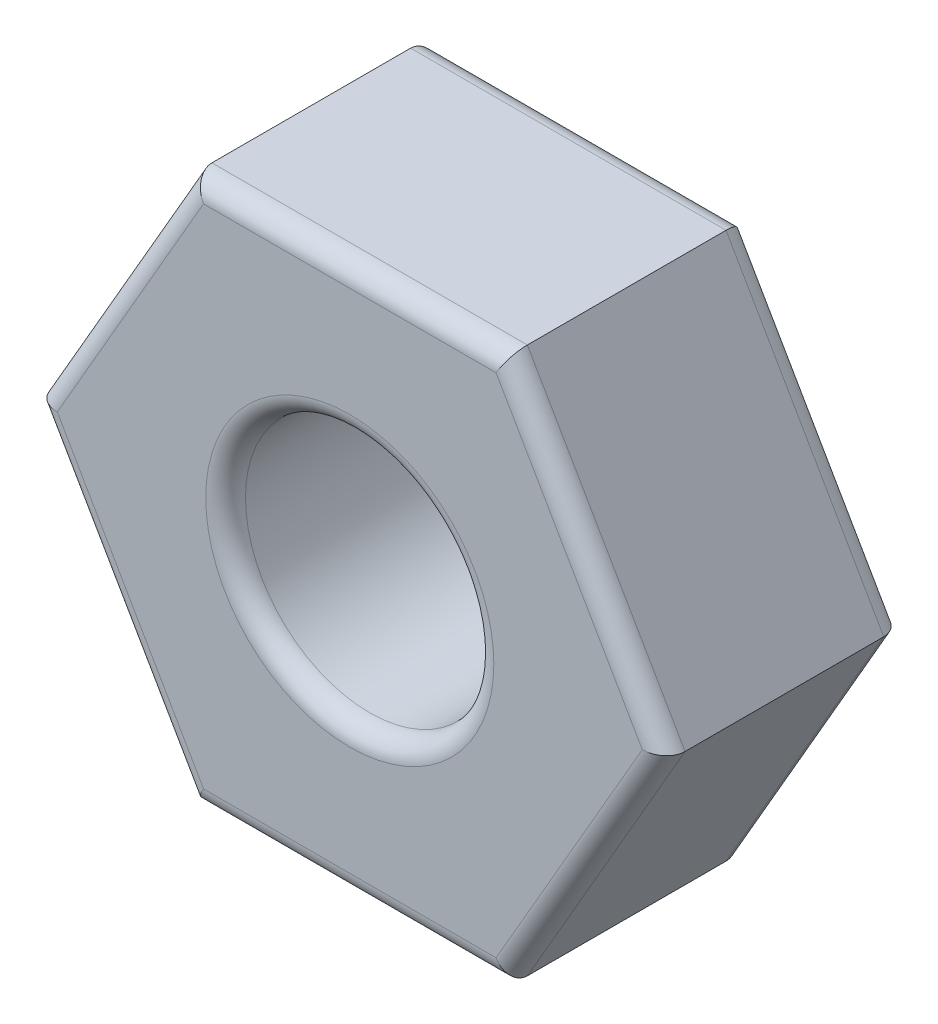
SolidWorks part; units mm, degrees
ref_plane "Front Plane" through (0, 0, 0) normal (0, 0, 1) x (1, 0, 0)
ref_plane "Top Plane" through (0, 0, 0) normal (0, 1, 0) x (1, 0, 0)
ref_plane "Right Plane" through (0, 0, 0) normal (1, 0, 0) x (0, 0, -1)
sketch "Sketch1" plane through (0, 0, 0) normal (0, 0, 1) x (1, 0, 0)
  line L1 (3.1754, 0) -> (1.5877, 2.75)
  line L2 (1.5877, 2.75) -> (-1.5877, 2.75)
  line L3 (-1.5877, 2.75) -> (-3.1754, 0)
  line L4 (-3.1754, 0) -> (-1.5877, -2.75)
  line L5 (-1.5877, -2.75) -> (1.5877, -2.75)
  line L6 (1.5877, -2.75) -> (3.1754, 0)
  circle A0 centre (0, 0) radius 2.75 construction
  circle A1 centre (0, 0) radius 1.25
  dimension "D1" = 5.5
  dimension "D2" = 2.5
extrude "Boss-Extrude1" add sketch "Sketch1" along normal blind 2.4
fillet "Fillet1" radius 0.2 14 edges at (1.25, 0, 2.4) (0, -2.75, 2.4) (-2.3816, -1.375, 2.4) (-2.3816, 1.375, 2.4) (0, 2.75, 2.4) (2.3816, 1.375, 2.4) (2.3816, -1.375, 2.4) (1.25, 0, 0) (2.3816, 1.375, 0) (0, 2.75, 0) (-2.3816, 1.375, 0) (-2.3816, -1.375, 0) (0, -2.75, 0) (2.3816, -1.375, 0)
